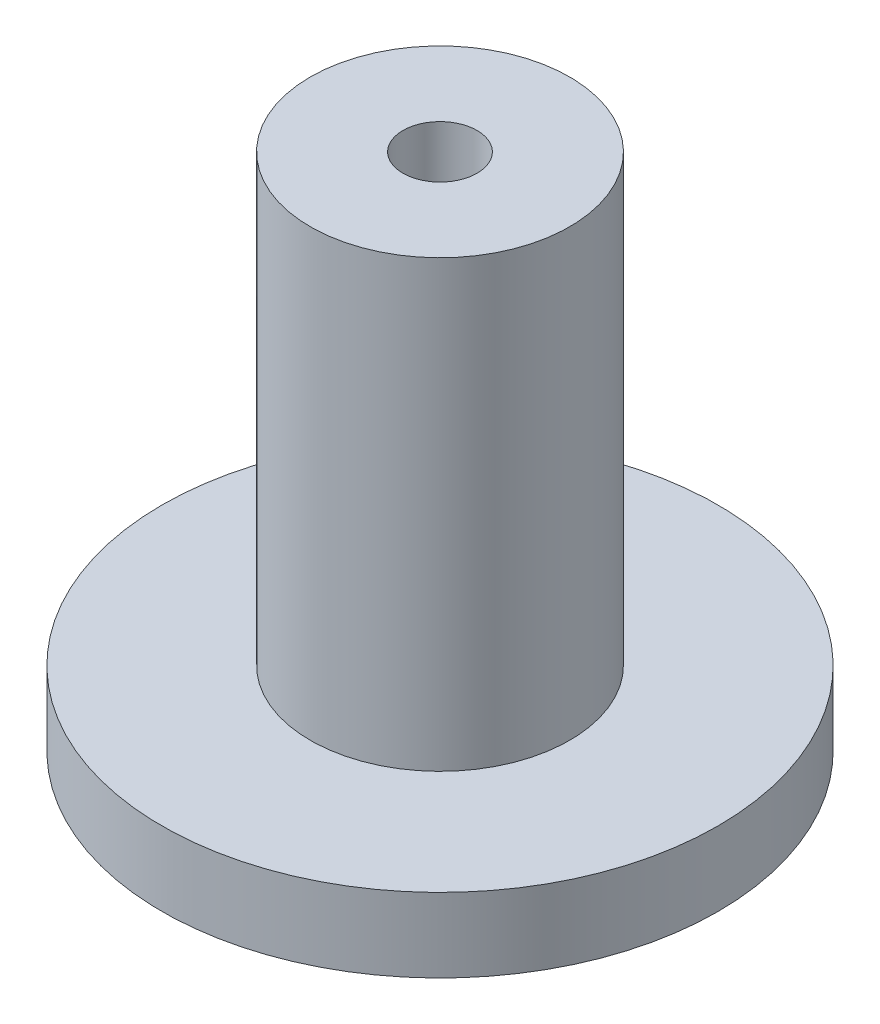
SolidWorks part; units mm, degrees
ref_plane "Front" through (0, 0, 0) normal (0, 0, 1) x (1, 0, 0)
ref_plane "Top" through (0, 0, 0) normal (0, 1, 0) x (1, 0, 0)
ref_plane "Right" through (0, 0, 0) normal (1, 0, 0) x (0, 0, -1)
sketch "Sketch1" plane through (0, 0, 0) normal (0, 0, 1) x (1, 0, 0)
  line L0 (0, 6.3183) -> (0, -11.6461) construction
  line L1 (11.9062, 0) -> (2.3813, 0)
  line L2 (2.3813, 0) -> (2.3813, 19.05)
  line L3 (2.3813, 19.05) -> (1.5875, 19.05)
  line L5 (1.5875, 22.225) -> (5.5563, 22.225)
  line L6 (5.5563, 22.225) -> (5.5563, 3.175)
  line L7 (5.5563, 3.175) -> (11.9062, 3.175)
  line L8 (11.9062, 3.175) -> (11.9062, 0)
  line L9 (1.5875, 19.05) -> (1.5875, 22.225)
  point P7 (1.5875, 17.1025)
  point P8 (13.2939, 3.175)
  dimension "D1" = 4.7625
  dimension "D2" = 3.175
  dimension "D3" = 3.175
  dimension "D4" = 3.175
  dimension "D5" = 22.225
  dimension "D6" = 6.35
revolve "Revolve1" add sketch "Sketch1" angle 360 about L0
